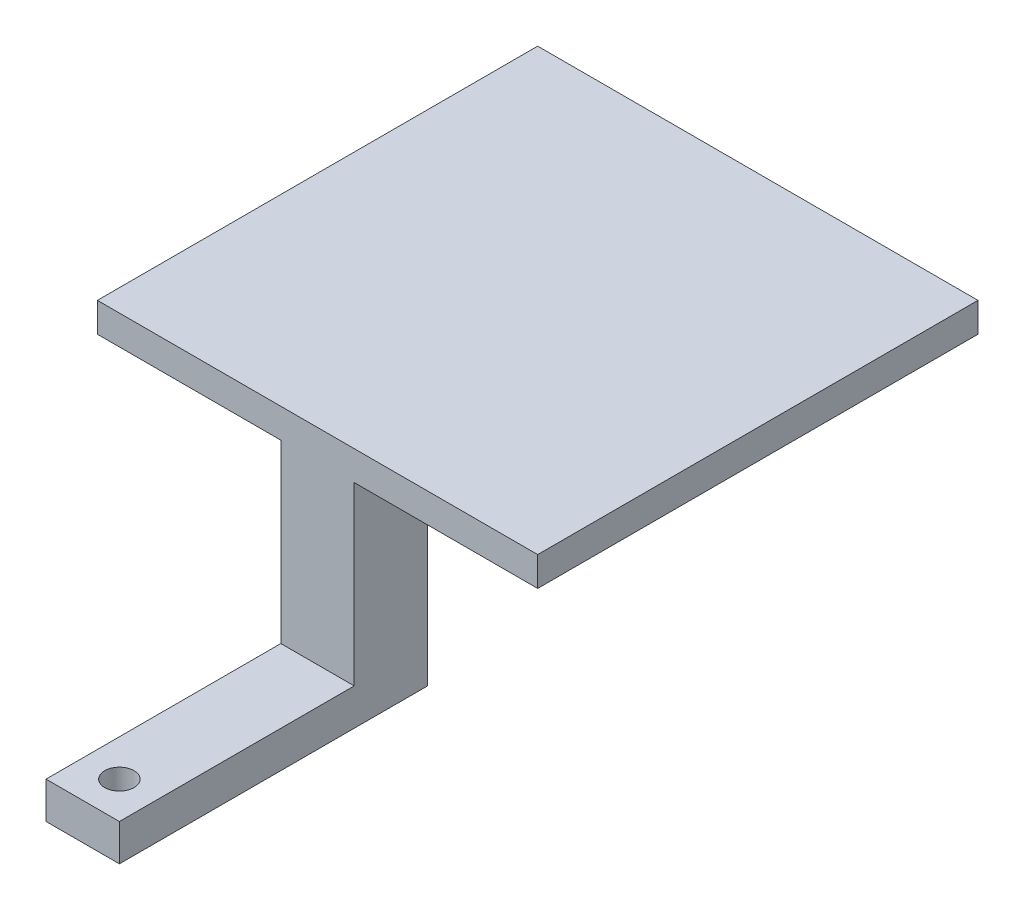
SolidWorks part; units mm, degrees
ref_plane "Front Plane" through (0, 0, 0) normal (0, 0, 1) x (1, 0, 0)
ref_plane "Top Plane" through (0, 0, 0) normal (0, 1, 0) x (1, 0, 0)
ref_plane "Right Plane" through (0, 0, 0) normal (1, 0, 0) x (0, 0, -1)
sketch "Sketch1" plane through (0, 0, 0) normal (0, 1, 0) x (1, 0, 0)
  line L1 (-15, 15) -> (15, 15)
  line L2 (-15, 15) -> (-15, -15)
  line L3 (-15, -15) -> (15, -15)
  line L4 (15, 15) -> (15, -15)
  line L5 (-15, 15) -> (15, -15) construction
  line L6 (-15, -15) -> (15, 15) construction
  point P0 (0, 0)
extrude "Boss-Extrude1" add sketch "Sketch1" along normal blind 2
sketch "Sketch2" plane through (0, 0, 0) normal (0, -1, 0) x (1, 0, 0)
  line L0 (0, 15) -> (-2.5, 15)
  line L1 (-15, 15) -> (15, 15) construction
  line L2 (-2.5, 15) -> (-2.5, 10)
  line L3 (-2.5, 10) -> (2.5, 10)
  line L4 (2.5, 10) -> (2.5, 15)
  line L5 (2.5, 15) -> (-2.5, 15)
  line M6 (15, 15) -> (-15, 15)
  dimension "D1" = 5
extrude "Boss-Extrude2" add sketch "Sketch2" along normal blind 14.5 contours L3 L4 L2 M6
sketch "Sketch3" plane through (0, 0, 15) normal (0, 0, 1) x (1, 0, 0)
  line L0 (-2.5, -14.5) -> (2.5, -14.5)
  line L1 (2.5, -14.5) -> (2.5, -12)
  line L2 (2.5, -14.5) -> (2.5, 0) construction
  line L3 (2.5, -12) -> (-2.5, -12)
  line L4 (-2.5, -14.5) -> (-2.5, 0) construction
  line L5 (-2.5, -12) -> (-2.5, -14.5)
extrude "Boss-Extrude3" add sketch "Sketch3" along normal blind 16
sketch "Sketch4" plane through (0, -14.5, 0) normal (0, -1, 0) x (-1, 0, 0)
  line L0 (-2.5, -10) -> (-2.5, -31) construction
  line L1 (2.5, -31) -> (-2.5, -31) construction
  circle A0 centre (0, -28.5) radius 1
  dimension "D1" = 2.5
  dimension "D2" = 2.5
extrude "Cut-Extrude1" cut sketch "Sketch4" against normal blind 5 contours A0
